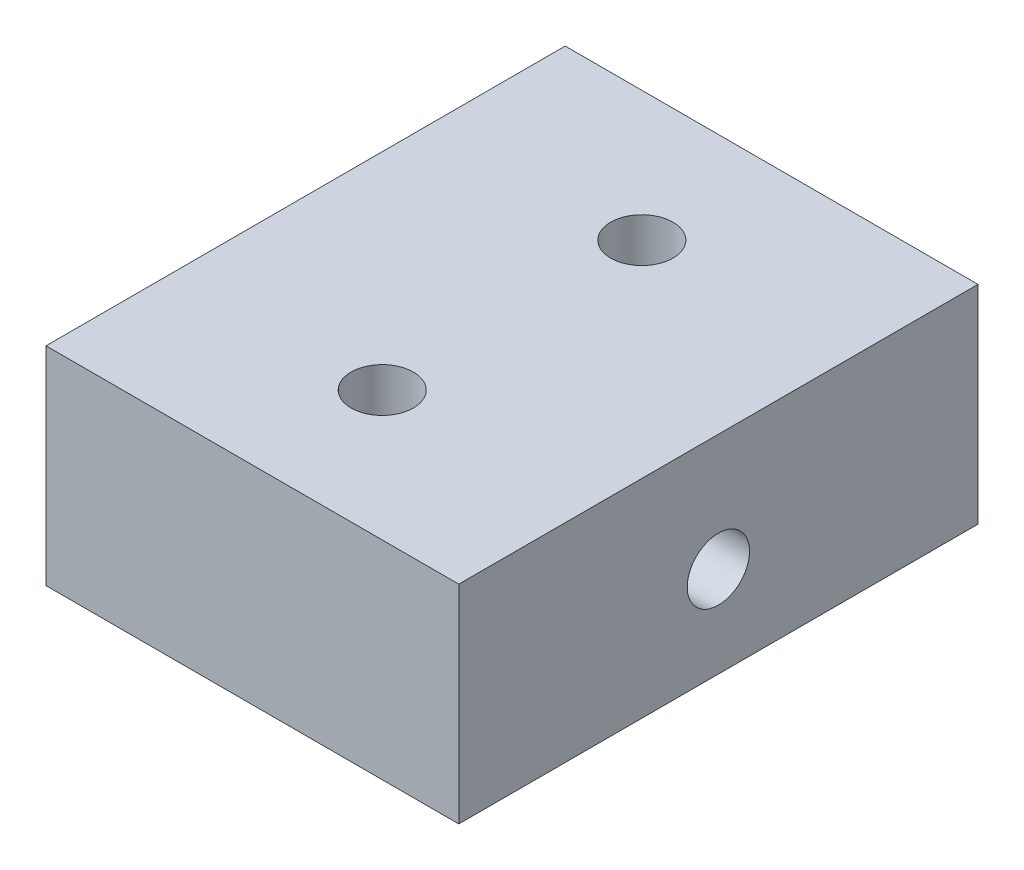
SolidWorks part; units mm, degrees
material "1060 Alloy"
ref_plane "Front Plane" through (0, 0, 0) normal (0, 0, 1) x (1, 0, 0)
ref_plane "Top Plane" through (0, 0, 0) normal (0, 1, 0) x (1, 0, 0)
ref_plane "Right Plane" through (0, 0, 0) normal (1, 0, 0) x (0, 0, -1)
sketch "Sketch1" plane through (0, 0, 0) normal (0, 0, 1) x (1, 0, 0)
  line L1 (0, 0) -> (15.9, 0)
  line L2 (0, 0) -> (0, 8)
  line L3 (0, 8) -> (15.9, 8)
  line L4 (15.9, 0) -> (15.9, 8)
  dimension "D1" = 15.9
  dimension "D2" = 8
extrude "Boss-Extrude1" add sketch "Sketch1" along normal blind 20
sketch "Sketch2" plane through (15.9, 0, 0) normal (1, 0, 0) x (0, 0, -1)
  line L0 (-20, 3.5) -> (0, 3.5) construction
  line L1 (-20, 0) -> (-20, 8) construction
  line L2 (0, 0) -> (0, 8) construction
  line L3 (-20, 0) -> (0, 0) construction
  circle A0 centre (-10, 3.5) radius 1.2
  dimension "D2" = 2.4
  dimension "D1" = 3.5
extrude "Cut-Extrude1" cut sketch "Sketch2" against normal through all
sketch "Sketch3" plane through (0, 8, 0) normal (0, 1, 0) x (1, 0, 0)
  line L0 (7.95, -20) -> (7.95, 0) construction
  line L1 (15.9, -20) -> (0, -20) construction
  line L2 (15.9, 0) -> (0, 0) construction
  line L3 (0, -10) -> (15.9, -10) construction
  line L4 (0, -20) -> (0, 0) construction
  line L5 (15.9, -20) -> (15.9, 0) construction
  circle A0 centre (7.95, -15) radius 1.2
  circle A1 centre (7.95, -5) radius 1.2
  dimension "D1" = 2.4
  dimension "D2" = 5
extrude "Cut-Extrude2" cut sketch "Sketch3" against normal through all
